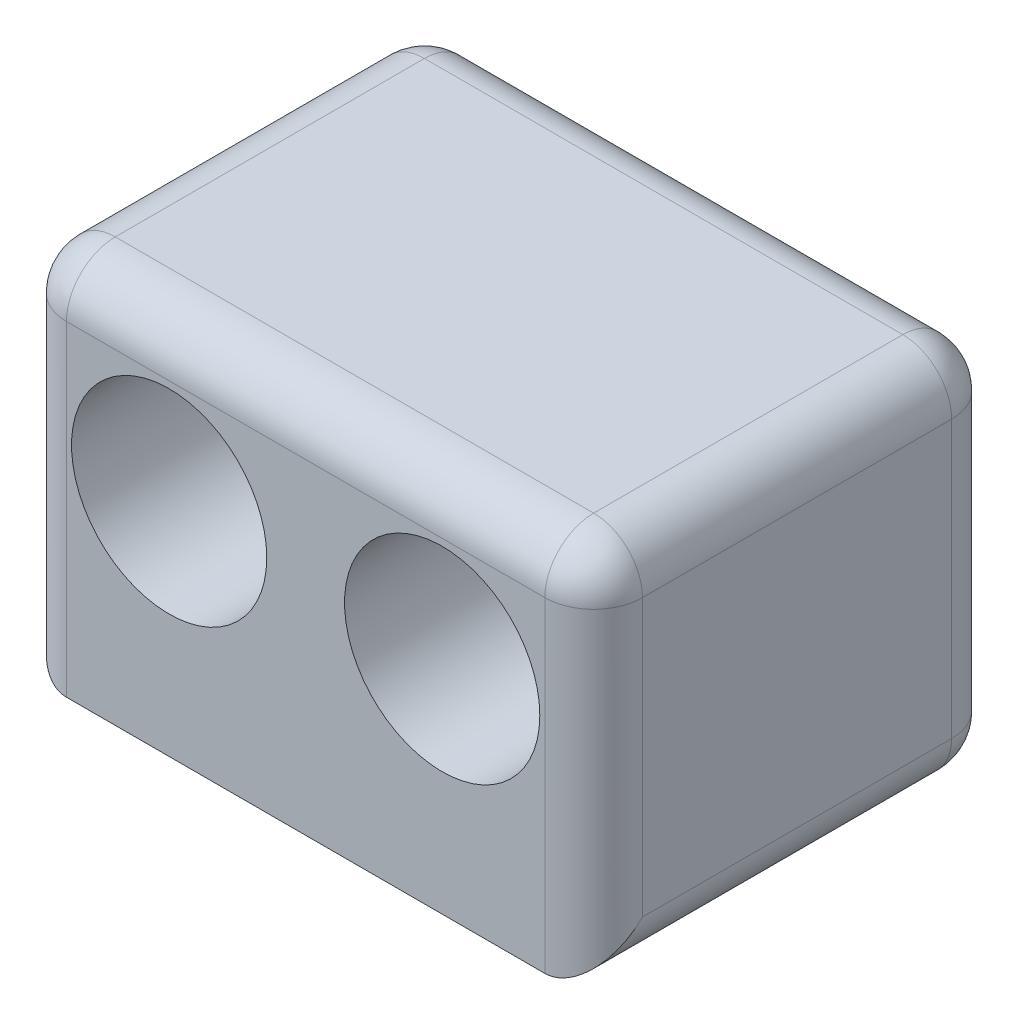
SolidWorks part; units mm, degrees
ref_plane "Plano frontal" through (0, 0, 0) normal (0, 0, 1) x (1, 0, 0)
ref_plane "Plano superior" through (0, 0, 0) normal (0, 1, 0) x (1, 0, 0)
ref_plane "Plano direito" through (0, 0, 0) normal (1, 0, 0) x (0, 0, -1)
sketch "Esboço1" plane through (0, 0, 0) normal (0, 0, 1) x (1, 0, 0)
  line L1 (-8.85, 5.75) -> (8.85, 5.75)
  line L2 (-8.85, 5.75) -> (-8.85, -5.75)
  line L3 (-8.85, -5.75) -> (8.85, -5.75)
  line L4 (8.85, 5.75) -> (8.85, -5.75)
  line L5 (-8.85, 5.75) -> (8.85, -5.75) construction
  line L6 (-8.85, -5.75) -> (8.85, 5.75) construction
  point P0 (0, 0)
  dimension "D1" = 17.7
  dimension "D2" = 11.5
extrude "Ressalto-extrusão1" add sketch "Esboço1" along normal blind 12.5
sketch "Esboço2" plane through (0, 0, 12.5) normal (0, 0, 1) x (1, 0, 0)
  line L0 (-4.195, 1.04) -> (4.195, 1.04) construction
  line L2 (-8.85, -5.75) -> (8.85, -5.75) construction
  circle A1 centre (4.195, 1.04) radius 3
  circle A2 centre (-4.195, 1.04) radius 3
  dimension "D4" = 6
  dimension "D5" = 6
  dimension "D1" = 6.79
  dimension "D2" = 8.39
  dimension "D3" = 4.195
extrude "Corte-extrusão1" cut sketch "Esboço2" against normal blind 10
fillet "Filete1" radius 1.5 11 edges at (0, 5.75, 12.5) (0, -5.75, 0) (-8.85, 0, 0) (0, 5.75, 0) (8.85, 0, 0) (8.85, 0, 12.5) (-8.85, 0, 12.5) (-8.85, -5.75, 6.25) (8.85, -5.75, 6.25) (-8.85, 5.75, 6.25) (8.85, 5.75, 6.25)
